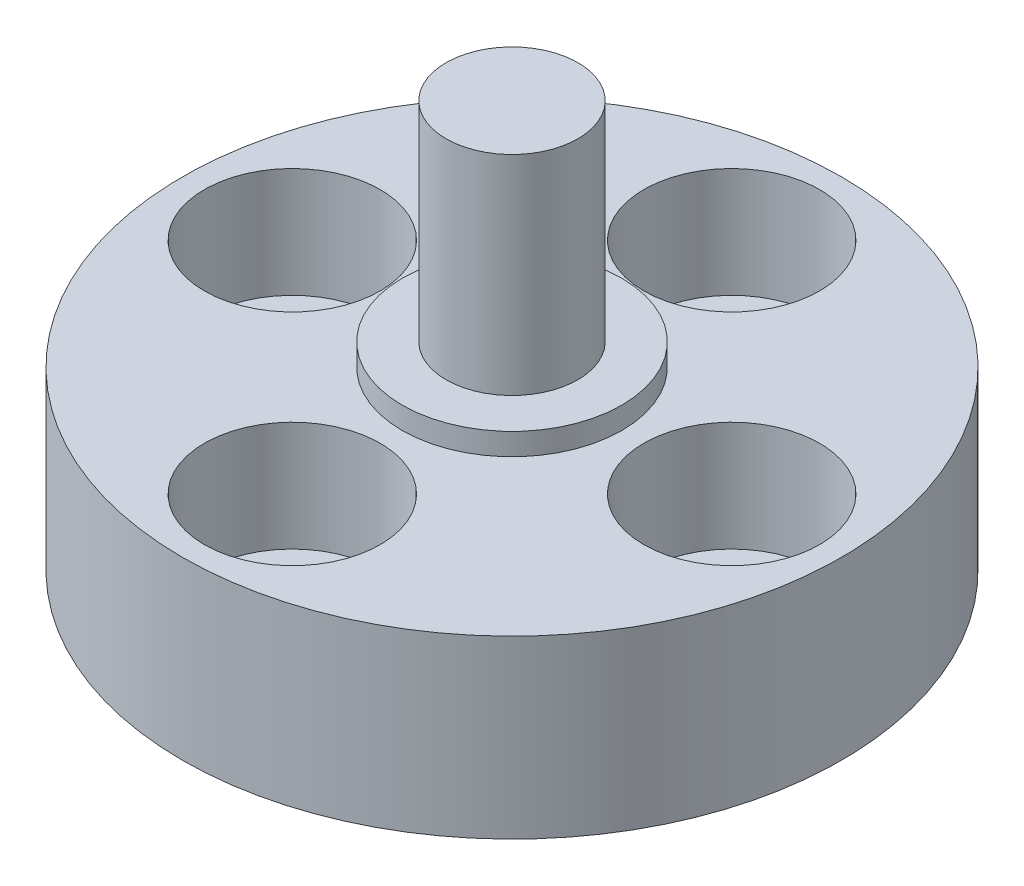
SolidWorks part; units mm, degrees
ref_plane "Front Plane" through (0, 0, 0) normal (0, 0, 1) x (1, 0, 0)
ref_plane "Top Plane" through (0, 0, 0) normal (0, 1, 0) x (1, 0, 0)
ref_plane "Right Plane" through (0, 0, 0) normal (1, 0, 0) x (0, 0, -1)
sketch "Sketch1" plane through (0, 0, 0) normal (0, 1, 0) x (1, 0, 0)
  circle A0 centre (0, 0) radius 15
  dimension "D1" = 30
extrude "Boss-Extrude1" add sketch "Sketch1" along normal blind 8
sketch "Sketch2" plane through (0, 8, 0) normal (0, 1, 0) x (1, 0, 0)
  circle A0 centre (0, 0) radius 5
  dimension "D1" = 10
extrude "Boss-Extrude2" add sketch "Sketch2" along normal blind 1
sketch "Sketch3" plane through (0, 9, 0) normal (0, 1, 0) x (1, 0, 0)
  circle A0 centre (0, 0) radius 3
  dimension "D1" = 6
extrude "Boss-Extrude3" add sketch "Sketch3" along normal blind 9.5
hole_wizard "Hole1" positions "Sketch7" profile "Sketch6" legacy end condition through all
sketch "Sketch7" plane through (0, 8, 0) normal (0, 1, 0) x (1, 0, 0)
  point P0 (-10, 0)
  point P2 (0, 10)
  point P4 (10, 0)
  point P6 (0, -10)
  dimension "D1" = 10
  dimension "D2" = 10
  dimension "D3" = 10
  dimension "D4" = 10
sketch "Sketch6" plane through (-10, 8, 0) normal (1, 0, 0) x (0, 0, 1)
  line L0 (0, 0) -> (0, 8)
  line L1 (0, 8) -> (2, 8)
  line L2 (2, 8) -> (2, 5)
  line L3 (2, 5) -> (4, 5)
  line L4 (4, 5) -> (4, 0)
  line L5 (4, 0) -> (0, 0)
  line L6 (0, 110) -> (0, -10) construction
  dimension "Diameter" = 4
  dimension "Depth" = 8
  dimension "C-Bore Diameter" = 8
  dimension "C-Bore Depth" = 5
